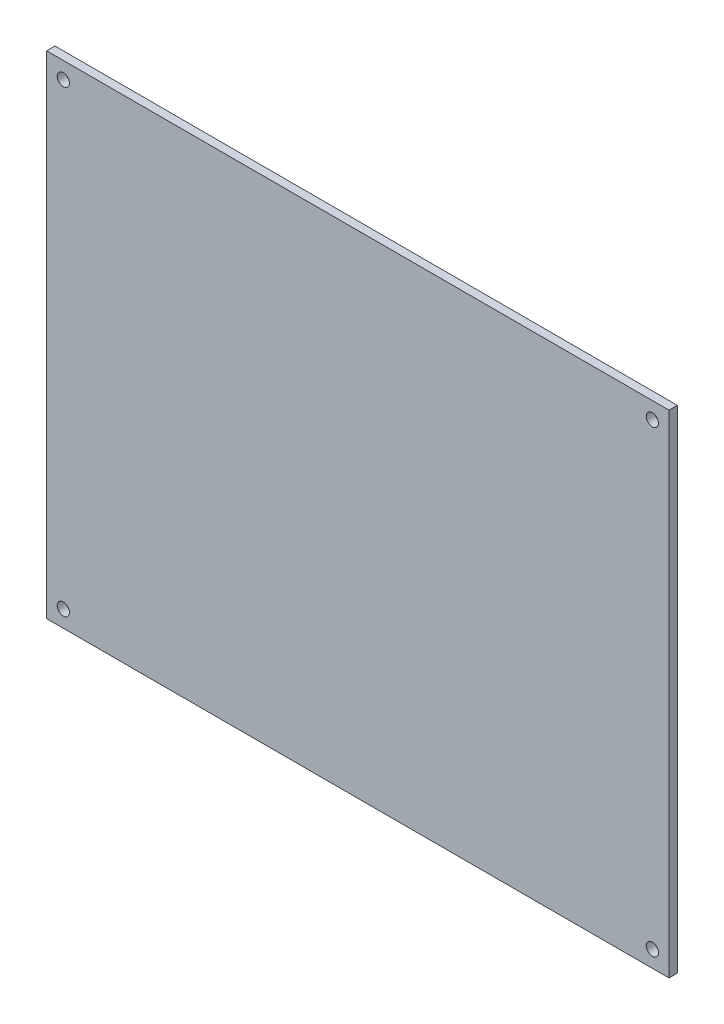
SolidWorks part; units mm, degrees
ref_plane "Front Plane" through (0, 0, 0) normal (0, 0, 1) x (1, 0, 0)
ref_plane "Top Plane" through (0, 0, 0) normal (0, 1, 0) x (1, 0, 0)
ref_plane "Right Plane" through (0, 0, 0) normal (1, 0, 0) x (0, 0, -1)
sketch "Sketch1" plane through (0, 0, 0) normal (0, 0, 1) x (1, 0, 0)
  line L1 (-56, -44.25) -> (56, -44.25)
  line L2 (-56, -44.25) -> (-56, 44.25)
  line L3 (-56, 44.25) -> (56, 44.25)
  line L4 (56, -44.25) -> (56, 44.25)
  line L5 (-56, -44.25) -> (56, 44.25) construction
  line L6 (-56, 44.25) -> (56, -44.25) construction
  point P0 (0, 0)
  dimension "D1" = 112
  dimension "D2" = 88.5
extrude "Boss-Extrude1" add sketch "Sketch1" along normal blind 1.5
sketch "Sketch2" plane through (0, 0, 1.5) normal (0, 0, 1) x (1, 0, 0)
  line L0 (-56, 44.25) -> (-56, -44.25) construction
  line L1 (-53, -41.25) -> (53, -41.25) construction
  line L2 (-53, -41.25) -> (-53, 41.25) construction
  line L3 (-53, 41.25) -> (53, 41.25) construction
  line L4 (53, -41.25) -> (53, 41.25) construction
  line L5 (-53, -41.25) -> (53, 41.25) construction
  line L6 (-53, 41.25) -> (53, -41.25) construction
  line L7 (56, 44.25) -> (-56, 44.25) construction
  circle A0 centre (-53, 41.25) radius 1.1
  circle A1 centre (53, 41.25) radius 1.1
  circle A2 centre (53, -41.25) radius 1.1
  circle A3 centre (-53, -41.25) radius 1.1
  point P0 (0, 0)
  dimension "D1" = 2.2
  dimension "D2" = 3
  dimension "D3" = 3
extrude "Cut-Extrude1" cut sketch "Sketch2" against normal through all
